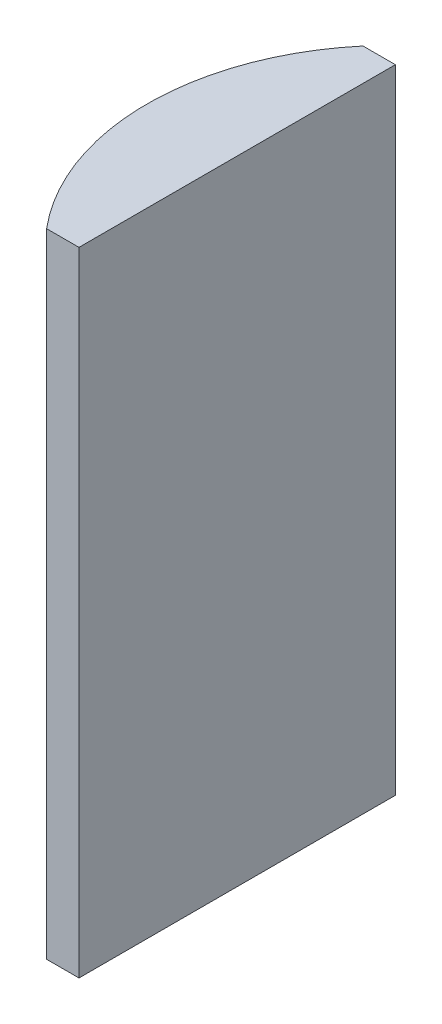
SolidWorks part; units mm, degrees
ref_plane "前视基准面" through (0, 0, 0) normal (0, 0, 1) x (1, 0, 0)
ref_plane "上视基准面" through (0, 0, 0) normal (0, 1, 0) x (1, 0, 0)
ref_plane "右视基准面" through (0, 0, 0) normal (1, 0, 0) x (0, 0, -1)
sketch "草图1" plane through (0, 0, 0) normal (0, 1, 0) x (1, 0, 0)
  line L0 (10.7432, 0) -> (-607.0701, 0) construction
  line L1 (-7.5006, 10) -> (-5.4548, 10)
  line L2 (-7.5006, -10) -> (-5.4548, -10)
  line L3 (-5.4548, 10) -> (-5.4548, -10)
  arc A0 (-7.5006, 10) -> (-7.5006, -10) centre (4.3552, 0) ccw
  point P19 (-11.1548, 0)
  point P20 (-5.4548, 0)
  dimension "D2" = 10
  dimension "D3" = 15.51
  dimension "D4" = 5.7
  dimension "D1" = 10
extrude "凸台-拉伸1" add sketch "草图1" along normal blind 40
